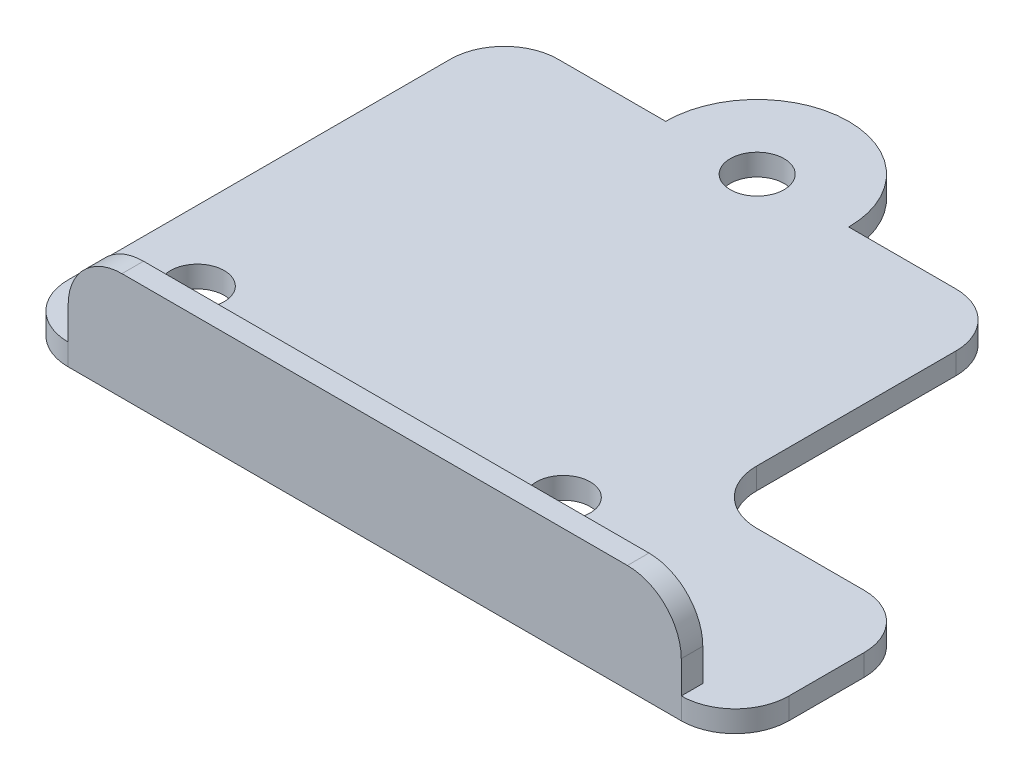
SolidWorks part; units mm, degrees
ref_plane "Front Plane" through (0, 0, 0) normal (0, 0, 1) x (1, 0, 0)
ref_plane "Top Plane" through (0, 0, 0) normal (0, 1, 0) x (1, 0, 0)
ref_plane "Right Plane" through (0, 0, 0) normal (1, 0, 0) x (0, 0, -1)
sketch "Sketch1" plane through (0, 0, 0) normal (0, 1, 0) x (1, 0, 0)
  line L0 (0, -19.6634) -> (0, 25.8466) construction
  line L1 (-18.5, 25.8466) -> (-8.5, 25.8466)
  line L2 (-23.5, 20.8466) -> (-23.5, -14.6634)
  line L3 (-18.5, -19.6634) -> (0, -19.6634)
  line L4 (8.5, 25.8466) -> (18.4573, 25.8466)
  line L6 (23.4573, -19.6634) -> (0, -19.6634)
  line L7 (23.4573, -19.6634) -> (23.4573, -2.6634) construction
  line L8 (23.4573, 20.8466) -> (23.4573, 2.3366)
  line L9 (23.4573, -19.6634) -> (38.4573, -19.6634)
  line L10 (43.4573, -14.6634) -> (43.4573, -7.6634)
  line L11 (38.4573, -2.6634) -> (28.4573, -2.6634)
  circle A0 centre (0, 25.8466) radius 8.5 construction
  circle A1 centre (-15, 25.8466) radius 8.5 construction
  circle A2 centre (15, 25.8466) radius 8.5 construction
  arc A3 (-8.5, 25.8466) -> (8.5, 25.8466) centre (0, 25.8466) cw
  arc A4 (18.4573, 25.8466) -> (23.4573, 20.8466) centre (18.4573, 20.8466) cw
  arc A5 (-18.5, 25.8466) -> (-23.5, 20.8466) centre (-18.5, 20.8466) ccw
  arc A6 (-23.5, -14.6634) -> (-18.5, -19.6634) centre (-18.5, -14.6634) ccw
  arc A7 (38.4573, -19.6634) -> (43.4573, -14.6634) centre (38.4573, -14.6634) ccw
  arc A8 (43.4573, -7.6634) -> (38.4573, -2.6634) centre (38.4573, -7.6634) ccw
  arc A9 (23.4573, 2.3366) -> (28.4573, -2.6634) centre (28.4573, 2.3366) ccw
  circle A10 centre (17, -9.1634) radius 7.5 construction
  circle A11 centre (-17, -9.1634) radius 7.5 construction
  circle A12 centre (-17, -9.1634) radius 2.5
  circle A13 centre (17, -9.1634) radius 2.5
  circle A14 centre (0, 25.8466) radius 2.5
  point P22 (-23.5, 25.8466)
  point P27 (43.4573, -19.6634)
  dimension "D2" = 17
  dimension "D7" = 5
  dimension "D8" = 15
  dimension "D9" = 17
  dimension "D10" = 10.5
  dimension "D12" = 10.5
  dimension "D13" = 5
  dimension "D1" = 45.51
  dimension "D3" = 15
  dimension "D4" = 15
  dimension "D5" = 17
  dimension "D6" = 20
  dimension "D11" = 17
extrude "Boss-Extrude1" add sketch "Sketch1" along normal blind 2
sketch "Sketch2" plane through (0, 2, 0) normal (0, 1, 0) x (1, 0, 0)
  line L0 (-18.5, -19.6634) -> (38.4573, -19.6634) construction
  line L1 (-18.5, -19.6634) -> (38.4573, -19.6634)
  line L2 (38.4573, -19.6634) -> (38.4573, -17.6634)
  line L3 (38.4573, -17.6634) -> (-18.5, -17.6634)
  line L4 (-18.5, -17.6634) -> (-18.5, -19.6634)
  dimension "D1" = 2
extrude "Boss-Extrude2" add sketch "Sketch2" along normal blind 8
fillet "Fillet1" radius 5 2 edges at (38.4573, 10, 18.6634) (-18.5, 10, 18.6634)
